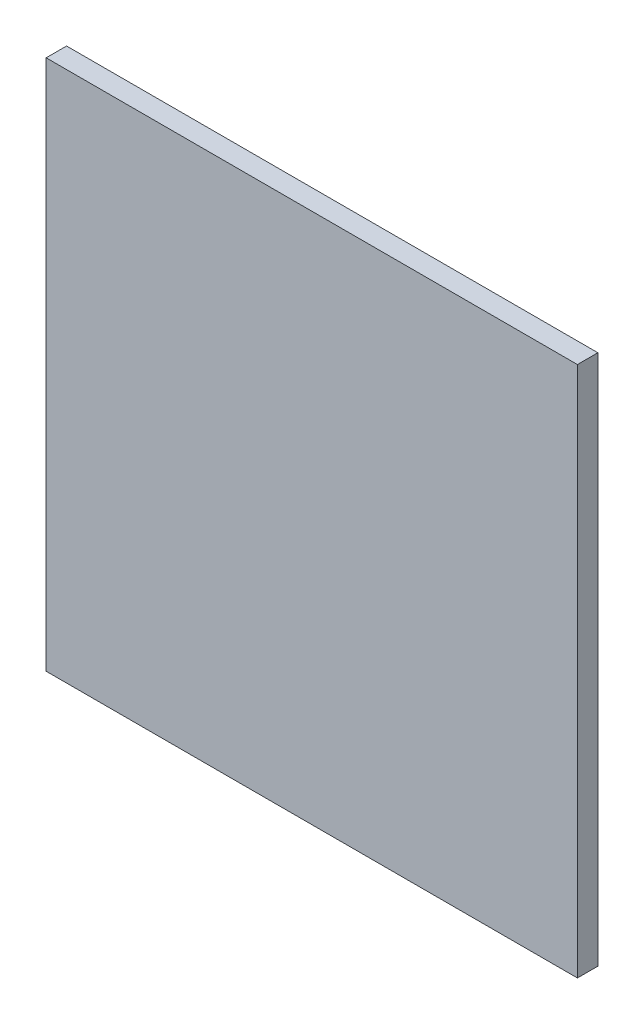
SolidWorks part; units mm, degrees
ref_plane "Piano frontale" through (0, 0, 0) normal (0, 0, 1) x (1, 0, 0)
ref_plane "Piano superiore" through (0, 0, 0) normal (0, 1, 0) x (1, 0, 0)
ref_plane "Piano destro" through (0, 0, 0) normal (1, 0, 0) x (0, 0, -1)
sketch "Schizzo3" plane through (0, 0, 0) normal (0, 0, 1) x (1, 0, 0)
  line L1 (65, -65) -> (-65, -65)
  line L2 (65, -65) -> (65, 65)
  line L3 (65, 65) -> (-65, 65)
  line L4 (-65, -65) -> (-65, 65)
  line L5 (65, -65) -> (-65, 65) construction
  line L6 (65, 65) -> (-65, -65) construction
  point P0 (0, 0)
  dimension "D1" = 130
  dimension "D2" = 130
extrude "Estrusione-Estrusione2" add sketch "Schizzo3" along normal blind 5
